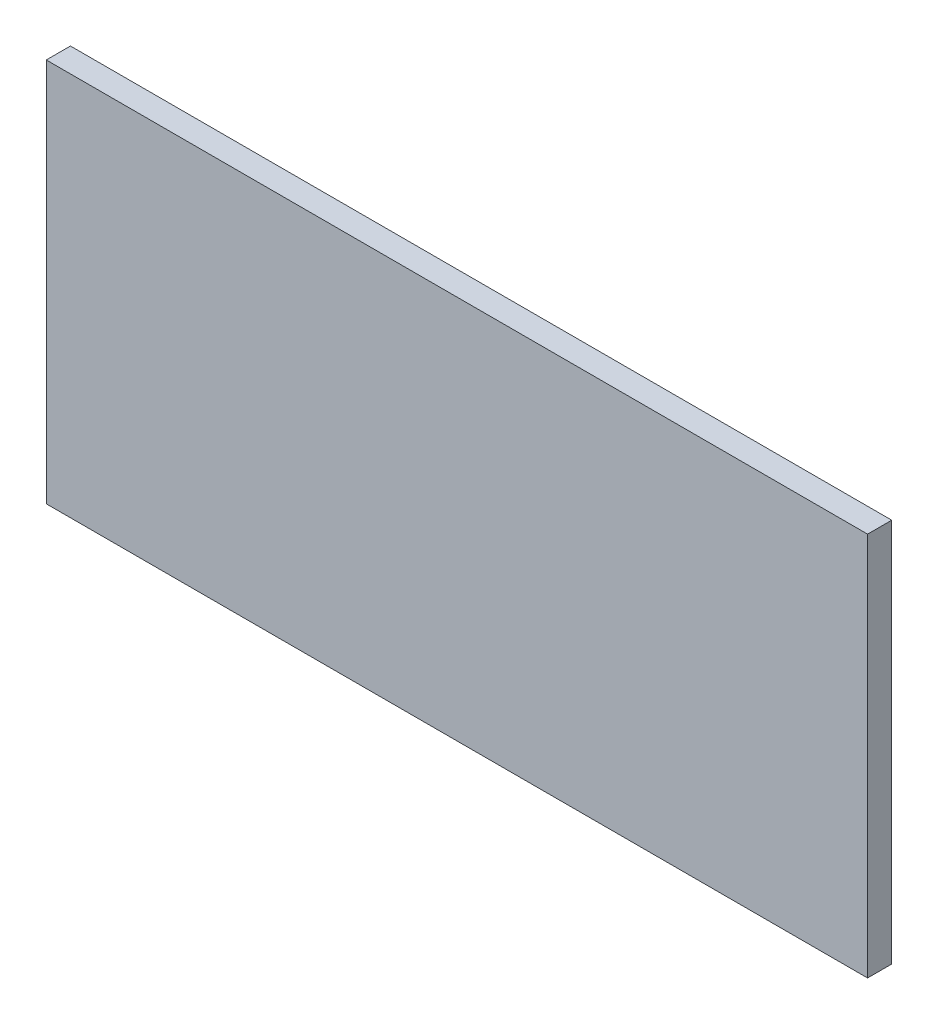
SolidWorks part; units mm, degrees
ref_plane "Front Plane" through (0, 0, 0) normal (0, 0, 1) x (1, 0, 0)
ref_plane "Top Plane" through (0, 0, 0) normal (0, 1, 0) x (1, 0, 0)
ref_plane "Right Plane" through (0, 0, 0) normal (1, 0, 0) x (0, 0, -1)
sketch "Sketch1" plane through (0, 0, 0) normal (0, 0, 1) x (1, 0, 0)
  line L1 (104.775, 0) -> (-3.175, 0)
  line L2 (104.775, 0) -> (104.775, -50.525)
  line L3 (104.775, -50.525) -> (-3.175, -50.525)
  line L4 (-3.175, 0) -> (-3.175, -50.525)
extrude "Boss-Extrude1" add sketch "Sketch1" along normal blind 3.175
